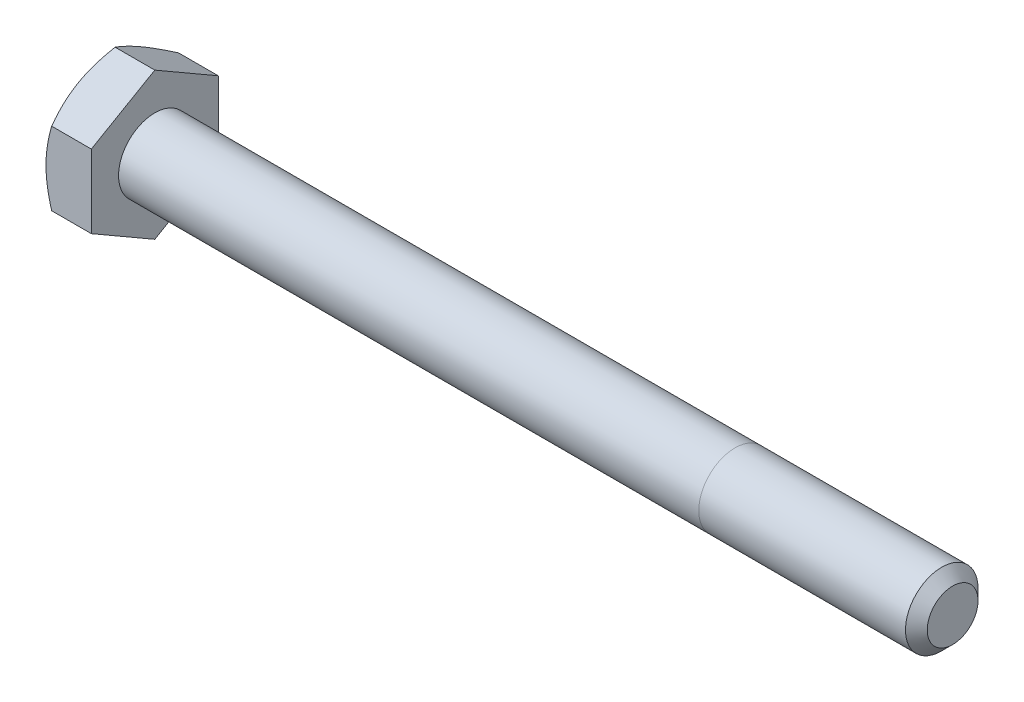
SolidWorks part; units mm, degrees
material "Alloy Steel"
ref_plane "Front Plane" through (0, 0, 0) normal (0, 0, 1) x (1, 0, 0)
ref_plane "Top Plane" through (0, 0, 0) normal (0, 1, 0) x (1, 0, 0)
ref_plane "Right Plane" through (0, 0, 0) normal (1, 0, 0) x (0, 0, -1)
sketch "Sketch1" plane through (0, 0, 0) normal (0, 0, 1) x (1, 0, 0)
  line L0 (-36.9094, 0) -> (36.9094, 0) construction
  line L1 (36.9094, 3.175) -> (36.9094, -3.175) construction
  line L2 (-32.9406, 5.5562) -> (-32.9406, -5.5562) construction
  line L3 (-36.9094, 5.5562) -> (-36.9094, -5.5562) construction
  point P9 (-32.9406, 0)
  point P10 (32.4644, -3.175)
  dimension "D1" = 4.445
  dimension "Screw Dia" = 6.35
  dimension "Hex" = 11.1125
  dimension "Head Ht" = 3.9688
  dimension "Screw Lenght" = 69.85
ref_plane "Plane2" through (36.9094, 0, 0) normal (1, 0, 0) x (0, 0, -1)
sketch "Sketch5" plane through (36.9094, 0, 0) normal (1, 0, 0) x (0, 0, -1)
  circle A0 centre (0, 0) radius 3.175
extrude "Boss-Extrude3" add sketch "Sketch5" against normal up to vertex (69.85 mm away) up to point (-32.9406, 0, 0)
sketch "Sketch9" plane through (36.9094, 0, 0) normal (1, 0, 0) x (0, 0, -1)
  circle A1 centre (0, 0) radius 3.175
  circle A2 centre (0, 0) radius 3.175
  dimension "D1" = 0
curve "Helix/Spiral1" pitch 1.27 height 20.32 turns 16 parameters "Pitch"=1.27
chamfer "Chamfer1" distance 0.9525 angle 45 1 edges at (36.9094, 0, -3.175)
sketch "Sketch10" plane through (0, 0, 0) normal (0, 0, 1) x (1, 0, 0)
  line L0 (36.9094, 3.175) -> (37.3856, 2.3501)
  line L1 (37.3856, 2.3501) -> (37.5444, 2.3501)
  line L2 (37.5444, 2.3501) -> (38.0206, 3.175)
  line L3 (36.9094, 3.175) -> (38.0206, 3.175)
  line L4 (37.465, 3.175) -> (37.465, 2.3501) construction
  line L5 (37.1475, 2.7626) -> (37.7825, 2.7626) construction
  dimension "D1" = 60
  dimension "D2" = 0.1588
  dimension "D3" = 0.635
sketch "Sketch11" plane through (0, 0, 0) normal (0, 0, 1) x (1, 0, 0)
  line L0 (-32.9406, 3.175) -> (-32.9406, 0)
  line L1 (-32.9406, 0) -> (21.0344, 0)
  line L3 (21.0344, 0) -> (17.8594, 3.175)
  line L4 (-32.9406, 3.175) -> (17.8594, 3.175)
  dimension "D1" = 45
  dimension "MIn Thread" = 19.05
revolve "Revolve1" add sketch "Sketch11" angle 360 about L1
sketch "Sketch6" plane through (-32.9406, 0, 0) normal (-1, 0, 0) x (0, 0, 1)
  line L0 (0, 5.5562) -> (0, -5.5562) construction
  line L1 (5.5563, 3.2079) -> (0, 6.4158)
  line L2 (0, 6.4158) -> (-5.5562, 3.2079)
  line L3 (-5.5562, 3.2079) -> (-5.5562, -3.2079)
  line L4 (-5.5562, -3.2079) -> (0, -6.4158)
  line L5 (0, -6.4158) -> (5.5563, -3.2079)
  line L6 (5.5563, -3.2079) -> (5.5563, 3.2079)
  circle A0 centre (0, 0) radius 5.5563 construction
extrude "Boss-Extrude4" add sketch "Sketch6" along normal up to vertex (3.9688 mm away) up to point (-36.9094, -5.5562, 0)
sketch "Sketch7" plane through (-36.9094, 0, 0) normal (-1, 0, 0) x (0, 0, 1)
  circle A0 centre (0, 0) radius 5.5563 construction
  circle A1 centre (0, 0) radius 5.5563
sketch "Sketch8" plane through (-36.9094, 0, 0) normal (-1, 0, 0) x (0, 0, 1)
  circle A0 centre (0, 0) radius 5.5563 construction
  circle A1 centre (0, 0) radius 5.5563
extrude "Cut-Extrude3" cut sketch "Sketch8" against normal through all draft 60 flip side to cut
sketch "Sketch12" plane through (-36.9094, 0, 0) normal (-1, 0, 0) x (0, 0, 1)
  line L0 (0, 4.2783) -> (0, 2.3892) construction
  line L1 (0.1667, 4.2783) -> (0.1667, 2.3892)
  line L2 (-0.1667, 4.2783) -> (-0.1667, 2.3892)
  line L3 (0, 3.175) -> (0, -3.175) construction
  arc A0 (0.1667, 4.2783) -> (-0.1667, 4.2783) centre (0, 4.2783) ccw
  arc A1 (-0.1667, 2.3892) -> (0.1667, 2.3892) centre (0, 2.3892) ccw
  circle A3 centre (0, 0) radius 2.2225 construction
  circle A4 centre (0, 0) radius 4.445 construction
  point P2 (0, 3.3337)
  dimension "D1" = 4.445
  dimension "D3" = 8.89
  dimension "D2" = 0.3334
extrude "Cut-Extrude4" cut sketch "Sketch12" against normal blind 0.254
pattern_circular "CirPattern1" count 3 over 360 about axis through (0, 0, 0) along (1, 0, 0) of "Cut-Extrude4"
sketch "Sketch13" plane through (0, 0, 0) normal (0, 1, 0) x (1, 0, 0)
  line L0 (17.8594, 3.175) -> (17.8594, -3.175)
  line L1 (35.9569, 3.175) -> (-32.9406, 3.175) construction
  line L2 (-32.9406, -3.175) -> (35.9569, -3.175) construction
  line L3 (36.9094, -2.2225) -> (36.9094, 2.2225) construction
  point P6 (17.8594, 0)
  dimension "D1" = 19.05
split line "Split Line1"
equation "\"D2@Sketch10\" = \"Pitch@Helix/Spiral1\"*.125"
equation "\"D3@Sketch10\" = \"Pitch@Helix/Spiral1\"*.5"
equation "\"D3@Helix/Spiral1\" = \"MIn Thread@Sketch11\"+\"Pitch@Helix/Spiral1\""
equation "\"D1@Chamfer1\" = \"Pitch@Helix/Spiral1\"*.75"
equation "\"D1@Sketch12\" = \"Hex@Sketch1\"*.4"
equation "\"D3@Sketch12\" = \"Hex@Sketch1\"*.8"
equation "\"D2@Sketch12\" = \"Hex@Sketch1\"*.03"
equation "\"D1@Sketch1\" = \"Pitch@Helix/Spiral1\"*3.5"
